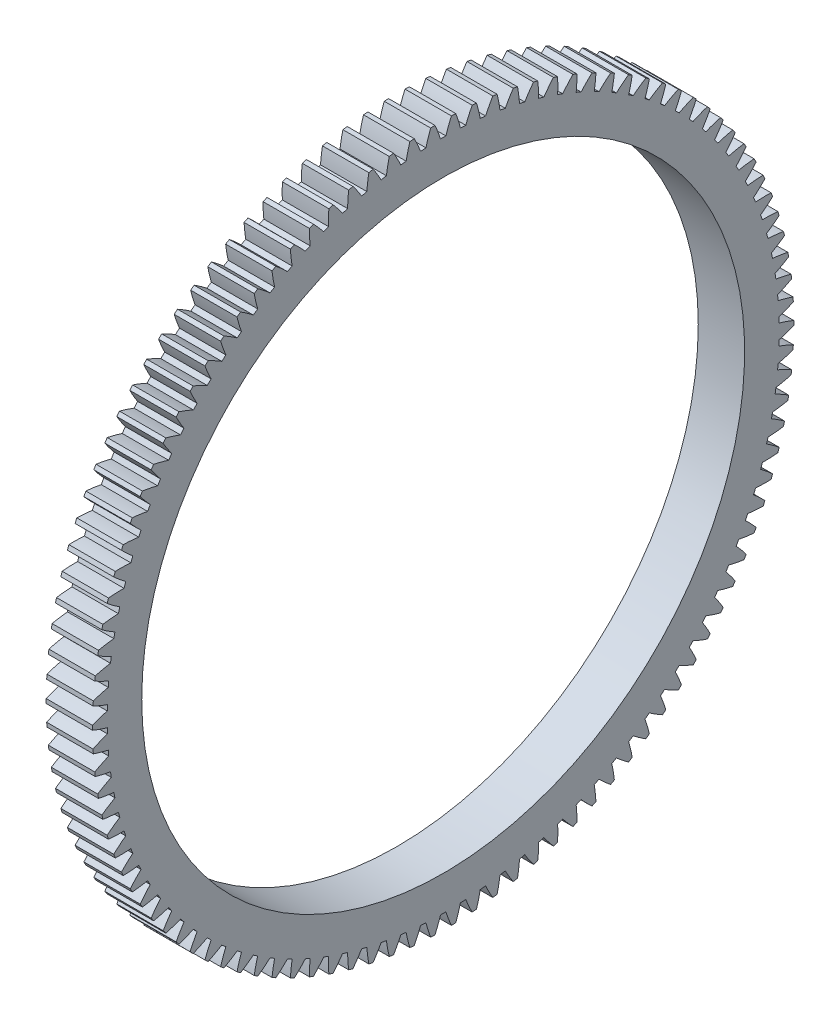
SolidWorks part; units mm, degrees
ref_plane "Plane1" through (0, 0, 0) normal (0, 0, 1) x (1, 0, 0)
ref_plane "Plane2" through (0, 0, 0) normal (0, 1, 0) x (1, 0, 0)
ref_plane "Plane3" through (0, 0, 0) normal (1, 0, 0) x (0, 0, -1)
sketch "HoldingSke" plane through (0, 0, 0) normal (0, 1, 0) x (1, 0, 0)
  line L0 (0, 0) -> (-0.3938, -1.3732)
  line L1 (-15, 0) -> (100, 0) construction
  line L2 (0, 0) -> (-2.1039, 2.3779)
  line L3 (0, 0) -> (-11.863, 4.5341)
  line L4 (0, 0) -> (-2.3804, 8.3015)
  line L5 (0, 0) -> (-46.8476, -17.4728)
  line L6 (0, 0) -> (-4.1448, -2.7965)
  line L7 (-2.1039, 2.3779) -> (8.6586, 51.2059)
  line L8 (-76.2, 54.61) -> (-71.3, 54.61)
  line L9 (-71.009, 38.7566) -> (-53.1078, 45.2721)
  line L10 (-76.2, 71.12) -> (104.1128, 71.12)
  line L11 (0, 0) -> (-5, 0)
  line L12 (-76.2, 101.6) -> (-76.173, 101.6)
  line L13 (24.9733, 27.94) -> (52.9518, 28.4284)
  line L14 (24.9733, 27.94) -> (24.9743, 27.94)
  line L15 (24.9733, 27.94) -> (100.4006, 29.5858)
  line L16 (-63.627, -0.7) -> (-12.827, -0.7)
  circle A0 centre (0, 0) radius 32.5
  circle A1 centre (0, 0) radius 36.224
  circle A2 centre (0, 0) radius 37.5
  circle A3 centre (0, 0) radius 32.5
  dimension "MHD" = 72.448
  dimension "Hub_dia" = 75
  dimension "Bore" = 65
  dimension "MBD" = 65
  dimension "Num_teeth" = 106
  dimension "Pitch" = 1.4286
  dimension "Overall_len" = 50
  dimension "Show_teeth" = 106
  dimension "Thickness" = 5
  dimension "OAL" = 50.0001
  dimension "T_dim" = 4.9
  dimension "Ap" = 20
  dimension "H" = 19.05
  dimension "Pitch_radius" = 180.3128
  dimension "Width" = 5
  dimension "Backlash" = 0.027
  dimension "Addendum_fac" = 1
  dimension "Dedendum_fac" = 1.25
  dimension "Clearance_fac" = 0.25
  dimension "Dedendum_add" = 0.001
  dimension "Module" = 0.7
sketch "BasProSke" plane through (0, 0, 0) normal (0, 1, 0) x (1, 0, 0)
  line L0 (-10, 0) -> (60, 0) construction
  line L1 (0, 0) -> (0, 37.8)
  line L2 (0, 0) -> (5, 0)
  line L3 (5, 0) -> (5, 37.8)
  line L4 (5, 37.8) -> (0, 37.8)
  dimension "Thickness" = 5
  dimension "Diameter" = 75.6
revolve "Base-Revolve" add sketch "BasProSke" angle 360 about L0
sketch "TooCutSke" plane through (0, 0, 0) normal (1, 0, 0) x (0, 0, -1)
  line L1 (0, 0) -> (0, 107) construction
  line L2 (0, 0) -> (-0.597, 37.0952) construction
  line L3 (0, 0) -> (-2.1986, 74.1606) construction
  line L4 (-0.597, 37.0952) -> (-1.0993, 37.0803) construction
  arc A0 (0.2899, 36.2228) -> (-0.2899, 36.2228) centre (0, 0) ccw
  arc A1 (0.8978, 37.8147) -> (-0.8978, 37.8147) centre (0, 0) ccw
  circle A2 centre (0, 0) radius 37.1 construction
  circle A3 centre (0, 0) radius 34.8626 construction
  arc A4 (-0.2899, 36.2228) -> (-0.8978, 37.8147) centre (-14.4347, 31.7339) ccw
  arc A5 (0.8978, 37.8147) -> (0.2899, 36.2228) centre (14.4347, 31.7339) ccw
  dimension "Root_dia" = 72.448
  dimension "Overcut_dia" = 75.6508
  dimension "Pitch_dia" = 74.2
  dimension "Base_dia" = 69.7252
  dimension "Flank_rad" = 14.84
  dimension "Half_ang" = 1.698
  dimension "Half_CT" = 0.5025
extrude "ToothCut" cut sketch "TooCutSke" along normal through all
fillet "Breaks" [suppressed] radius 0.014
fillet "RootFillets" [suppressed] radius 0.176
pattern_circular "TeethCuts" count 106 every 3.396 about axis through (-10, 0, 0) along (1, 0, 0) of "ToothCut", "RootFillets", "Breaks"
sketch "HubNeaOneSke" plane through (0, 0, 0) normal (-1, 0, 0) x (0, 0, 1)
  circle A0 centre (0, 0) radius 36.224
  dimension "Diameter" = 72.448
extrude "HubNearOne" [suppressed] add sketch "HubNeaOneSke" along normal blind 45.0001
sketch "HubNeaBotSke" plane through (0, 0, 0) normal (-1, 0, 0) x (0, 0, 1)
  circle A0 centre (0, 0) radius 36.224
  dimension "Diameter" = 72.448
extrude "HubNearBoth" [suppressed] add sketch "HubNeaBotSke" along normal blind 22.5
ref_plane "FarPln" through (5, 0, 0) normal (1, 0, 0) x (0, 0, -1)
sketch "HubFarSke" plane through (5, 0, 0) normal (1, 0, 0) x (0, 0, -1)
  circle A0 centre (0, 0) radius 36.224
  dimension "Diameter" = 72.448
extrude "HubFar" [suppressed] add sketch "HubFarSke" along normal blind 22.5
sketch "BorSke" plane through (0, 0, 0) normal (1, 0, 0) x (0, 0, -1)
  circle A0 centre (0, 0) radius 32.5
  dimension "Diameter" = 65
extrude "Bore" cut sketch "BorSke" along normal mid plane 100.0001
sketch "KeySke" plane through (0, 0, 0) normal (1, 0, 0) x (0, 0, -1)
  line L0 (-10, 0) -> (-10, 37.4)
  line L1 (-10, 37.4) -> (10, 37.4)
  line L2 (10, 37.4) -> (10, 0)
  line L3 (0, 0) -> (0, 34) construction
  line L4 (-10, 0) -> (10, 0)
  dimension "Offset" = 37.4
  dimension "Width" = 20
extrude "Keyway" [suppressed] cut sketch "KeySke" along normal mid plane 100.0001
pattern_circular "Keyway2" [suppressed] count 2 every 90 about axis through (-10, 0, 0) along (1, 0, 0)
equation "' \"Module@HoldingSke\" = 6.35"
equation "' \"Num_teeth@HoldingSke\" = 12"
equation "' \"Ap@HoldingSke\" =  20"
equation "' \"Ap@HoldingSke\" = 20"
equation "' \"Width@HoldingSke\" = 0.5 * 25.4"
equation "' \"Hub_dia@HoldingSke\"= 1 * 25.4"
equation "' \"Hub_dia@HoldingSke\" = 1 * 25.4"
equation "' \"Overall_len@HoldingSke\" = 1.0 * 25.4"
equation "' \"Bore@HoldingSke\" = 0.75 * 25.4"
equation "' \"T_dim@HoldingSke\" = 0.1 * 25.4"
equation "' \"Width@KeySke\" = 0.25 * 25.4"
equation "' \"Show_teeth@HoldingSke\" = 13"
equation "' \"Backlash@HoldingSke\" = 0.009 * 25.4"
equation "' \"Addendum_fac@HoldingSke\" = 1.0"
equation "' \"Dedendum_fac@HoldingSke\" = 1.25"
equation "' \"Dedendum_add@HoldingSke\" = 0.00005 * 25.4"
equation "' \"Clearance_fac@HoldingSke\" = 0.25"
equation "\"Pitch@HoldingSke\" = 1 / \"Module@HoldingSke\""
equation "\"Overcut_dia@TooCutSke\" = (\"Num_teeth@HoldingSke\" + 2 * \"Addendum_fac@HoldingSke\") / \"Pitch@HoldingSke\" + 0.002 * 25.4"
equation "\"Pitch_dia@TooCutSke\" = \"Num_teeth@HoldingSke\" / \"Pitch@HoldingSke\""
equation "\"Base_dia@TooCutSke\" = \"Num_teeth@HoldingSke\" / \"Pitch@HoldingSke\" * cos((\"Ap@HoldingSke\"  * 3.14159265 / 180))"
equation "\"Root_dia@TooCutSke\" = (\"Num_teeth@HoldingSke\" + 2) / \"Pitch@HoldingSke\" - 2 * (\"Addendum_fac@HoldingSke\" + \"Dedendum_fac@HoldingSke\") / \"Pitch@HoldingSke\" - \"Dedendum_add@HoldingSke\" * 2"
equation "\"Half_ang@TooCutSke\" = 180 / \"Num_teeth@HoldingSke\""
equation "\"Half_CT@TooCutSke\" = \"Num_teeth@HoldingSke\" / \"Pitch@HoldingSke\" * sin((3.14159265 / 2 / \"Num_teeth@HoldingSke\")) / 2 - 7 * \"Backlash@HoldingSke\" / 4"
equation "\"Flank_rad@TooCutSke\" = \"Num_teeth@HoldingSke\" / \"Pitch@HoldingSke\" / 5"
equation "\"Radius@RootFillets\" = \"Clearance_fac@HoldingSke\" / \"Pitch@HoldingSke\" + \"Dedendum_add@HoldingSke\""
equation "\"Break_rad@Breaks\" = 0.02 / \"Pitch@HoldingSke\""
equation "\"Thickness@HoldingSke\" = \"Width@HoldingSke\""
equation "\"OAL@HoldingSke\" = \"Thickness@HoldingSke\""
equation "\"MHD@HoldingSke\" = (\"Num_teeth@HoldingSke\" + 2) / \"Pitch@HoldingSke\" - 2 * (\"Addendum_fac@HoldingSke\" + \"Dedendum_fac@HoldingSke\")  / \"Pitch@HoldingSke\" - \"Dedendum_add@HoldingSke\" * 2"
equation "\"MBD@HoldingSke\" = (\"Num_teeth@HoldingSke\" + 2) / \"Pitch@HoldingSke\" - 2 * (\"Addendum_fac@HoldingSke\" + \"Dedendum_fac@HoldingSke\")  / \"Pitch@HoldingSke\" - \"Dedendum_add@HoldingSke\" * 2 - 0.002 * 25.4"
equation "\"MHD@HoldingSke\" = ((sgn( \"MHD@HoldingSke\" - \"Hub_dia@HoldingSke\" )-1)*( \"MHD@HoldingSke\" - \"Hub_dia@HoldingSke\" ))/-2+ \"Hub_dia@HoldingSke\""
equation "\"MBD@HoldingSke\" = ((sgn( \"MBD@HoldingSke\" - \"Bore@HoldingSke\" )-1)*( \"MBD@HoldingSke\" - \"Bore@HoldingSke\" ))/-2+ \"Bore@HoldingSke\""
equation "\"OAL@HoldingSke\" = ((sgn( \"OAL@HoldingSke\" - \"Overall_len@HoldingSke\" )+1)*( \"OAL@HoldingSke\" - \"Overall_len@HoldingSke\" ))/2 + \"Overall_len@HoldingSke\" + 0.000002 * 25.4"
equation "\"Num_teeth@TeethCuts\" = int( \"Show_teeth@HoldingSke\" ) + 1"
equation "\"Num_teeth@TeethCuts\" = ((sgn( \"Num_teeth@TeethCuts\" - \"Num_teeth@HoldingSke\" )-1)*( \"Num_teeth@TeethCuts\" - \"Num_teeth@HoldingSke\" ))/-2+ \"Num_teeth@HoldingSke\""
equation "\"Num_teeth@TeethCuts\" = ((sgn( \"Num_teeth@TeethCuts\" - 2.0)+1)*( \"Num_teeth@TeethCuts\" - 2.0))/2 +2.0"
equation "\"Angle@TeethCuts\" = 360.0 / \"Num_teeth@HoldingSke\""
equation "\"Diameter@BasProSke\" = (\"Num_teeth@HoldingSke\" + 2 * \"Addendum_fac@HoldingSke\") / \"Pitch@HoldingSke\""
equation "\"Thickness@BasProSke\"  = \"Thickness@HoldingSke\""
equation "' \"Fillet_rad@BasProSke\" =  \"Thickness@HoldingSke\" * 0.05"
equation "' \"Fillet_rad@BasProSke\" = \"Thickness@HoldingSke\" * 0.05"
equation "\"MHD@HoldingSke\" = ((sgn( \"MHD@HoldingSke\" - \"Root_dia@TooCutSke\" )-1)*( \"MHD@HoldingSke\" - \"Root_dia@TooCutSke\" ))/-2+ \"Root_dia@TooCutSke\""
equation "\"Diameter@HubNeaOneSke\" = \"MHD@HoldingSke\""
equation "\"Length@HubNearOne\" = \"OAL@HoldingSke\" - \"Thickness@BasProSke\""
equation "\"Diameter@HubNeaBotSke\" = \"MHD@HoldingSke\""
equation "\"Length@HubNearBoth\" = ( \"OAL@HoldingSke\" - \"Thickness@BasProSke\" ) / 2.0"
equation "\"Thickness@FarPln\" = \"Thickness@BasProSke\""
equation "\"Diameter@HubFarSke\" = \"MHD@HoldingSke\""
equation "\"Length@HubFar\" = ( \"OAL@HoldingSke\" - \"Thickness@BasProSke\" ) / 2.0"
equation "\"Diameter@BorSke\" = \"MBD@HoldingSke\""
equation "\"D1@Bore\" = \"OAL@HoldingSke\" * 2.0"
equation "\"D1@Keyway\" = \"OAL@HoldingSke\" * 2.0"
equation "\"Offset@KeySke\" = \"T_dim@HoldingSke\" + \"MBD@HoldingSke\" / 2.0"
